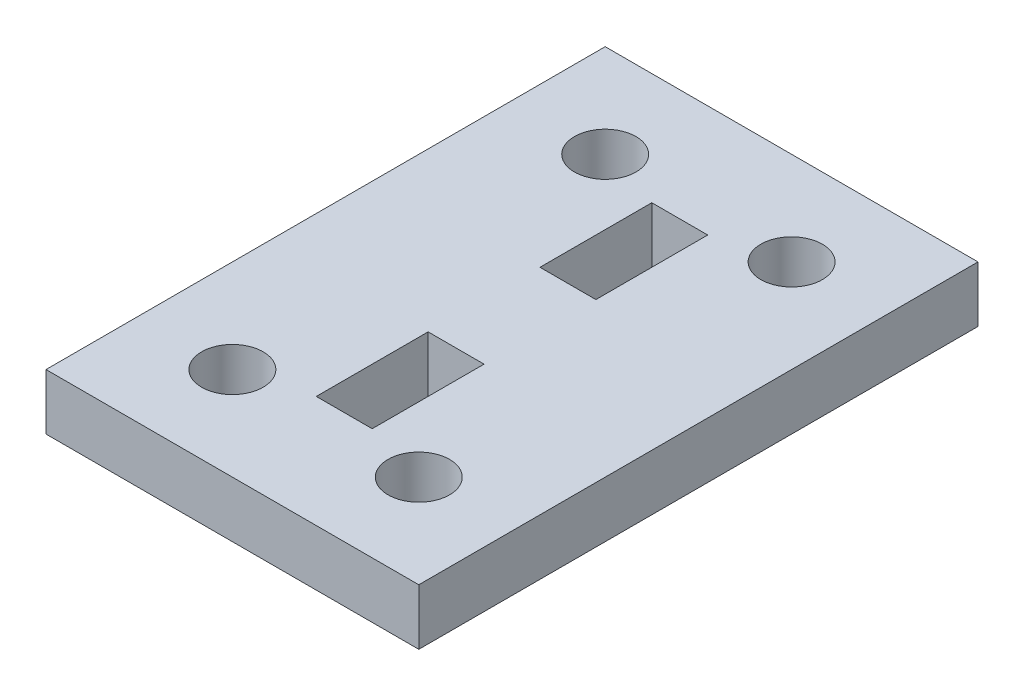
SolidWorks part; units mm, degrees
ref_plane "Ön Düzlem" through (0, 0, 0) normal (0, 0, 1) x (1, 0, 0)
ref_plane "Üst Düzlem" through (0, 0, 0) normal (0, 1, 0) x (1, 0, 0)
ref_plane "Sağ Düzlem" through (0, 0, 0) normal (1, 0, 0) x (0, 0, -1)
sketch "Sketch1" plane through (0, 0, 0) normal (0, 1, 0) x (1, 0, 0)
  line L1 (10, -15) -> (-10, -15)
  line L2 (10, -15) -> (10, 15)
  line L3 (10, 15) -> (-10, 15)
  line L4 (-10, -15) -> (-10, 15)
  line L5 (10, -15) -> (-10, 15) construction
  line L6 (10, 15) -> (-10, -15) construction
  line L7 (1.5, 9) -> (1.5, 3)
  line L8 (-1.5, 9) -> (1.5, 9)
  line L9 (-1.5, -9) -> (1.5, -9)
  line L10 (-1.5, -9) -> (-1.5, -3)
  line L11 (-1.5, -3) -> (1.5, -3)
  line L12 (1.5, -9) -> (1.5, -3)
  line L13 (-1.5, 9) -> (-1.5, 3)
  line L14 (-1.5, 3) -> (1.5, 3)
  circle A1 centre (-5, -10) radius 1.65
  circle A2 centre (5, -10) radius 1.65
  circle A3 centre (5, 10) radius 1.65
  circle A4 centre (-5, 10) radius 1.65
  point P0 (0, 0)
  dimension "D3" = 3
  dimension "D1" = 30
  dimension "D2" = 20
  dimension "D4" = 6
extrude "Boss-Extrude1" add sketch "Sketch1" along normal blind 3
